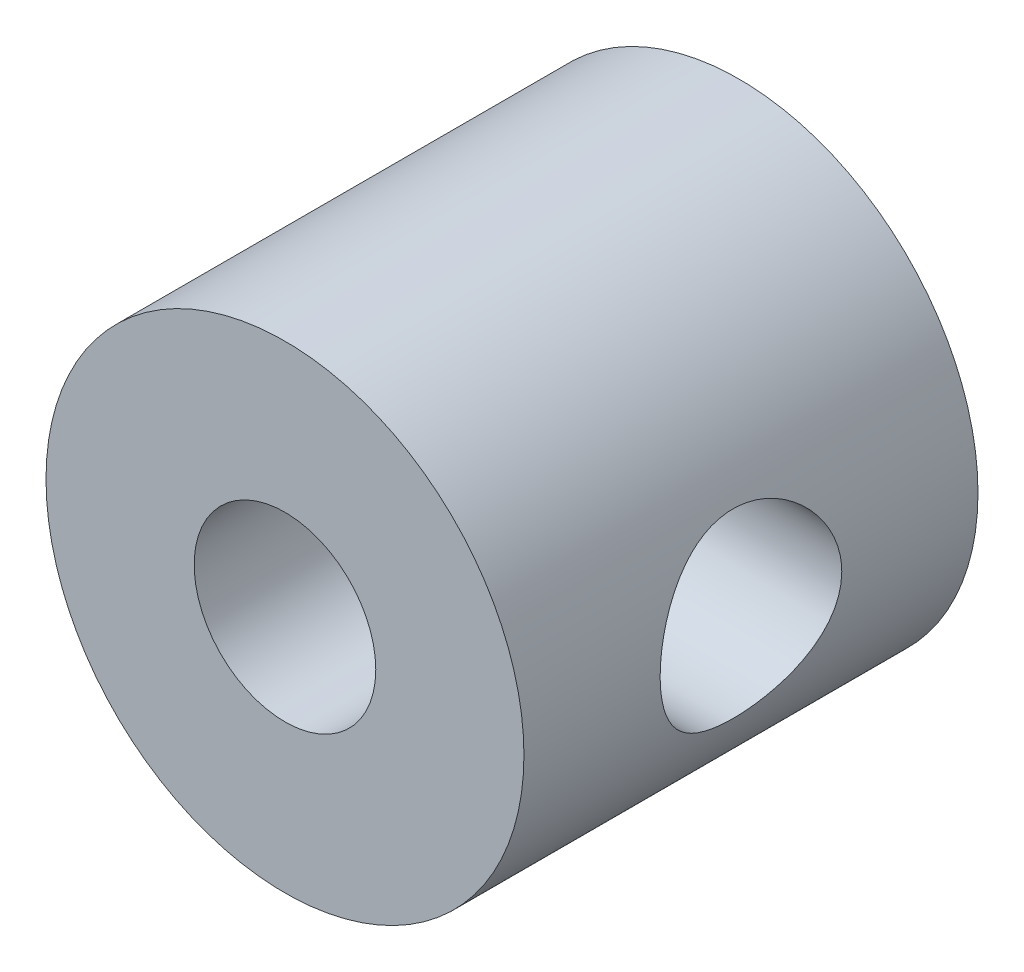
SolidWorks part; units mm, degrees
ref_plane "Front Plane" through (0, 0, 0) normal (0, 0, 1) x (1, 0, 0)
ref_plane "Top Plane" through (0, 0, 0) normal (0, 1, 0) x (1, 0, 0)
ref_plane "Right Plane" through (0, 0, 0) normal (1, 0, 0) x (0, 0, -1)
sketch "Sketch1" plane through (0, 0, 0) normal (0, 0, 1) x (1, 0, 0)
  circle A0 centre (0, 0) radius 5
  dimension "D1" = 10
extrude "Boss-Extrude1" add sketch "Sketch1" along normal blind 9.5
sketch "Sketch2" plane through (0, 0, 9.5) normal (0, 0, 1) x (1, 0, 0)
  circle A0 centre (0, 0) radius 1.9
  dimension "D1" = 3.8
extrude "Cut-Extrude1" cut sketch "Sketch2" against normal through all both and the other way through all
sketch "Sketch3" plane through (0, 0, 0) normal (1, 0, 0) x (0, 0, -1)
  line L0 (-9.5, 0) -> (0, 0) construction
  line L1 (-9.5, 5) -> (-9.5, -5) construction
  circle A0 centre (-4.75, 0) radius 1.9
  dimension "D1" = 3.8
extrude "Cut-Extrude2" cut sketch "Sketch3" against normal through all both and the other way through all
